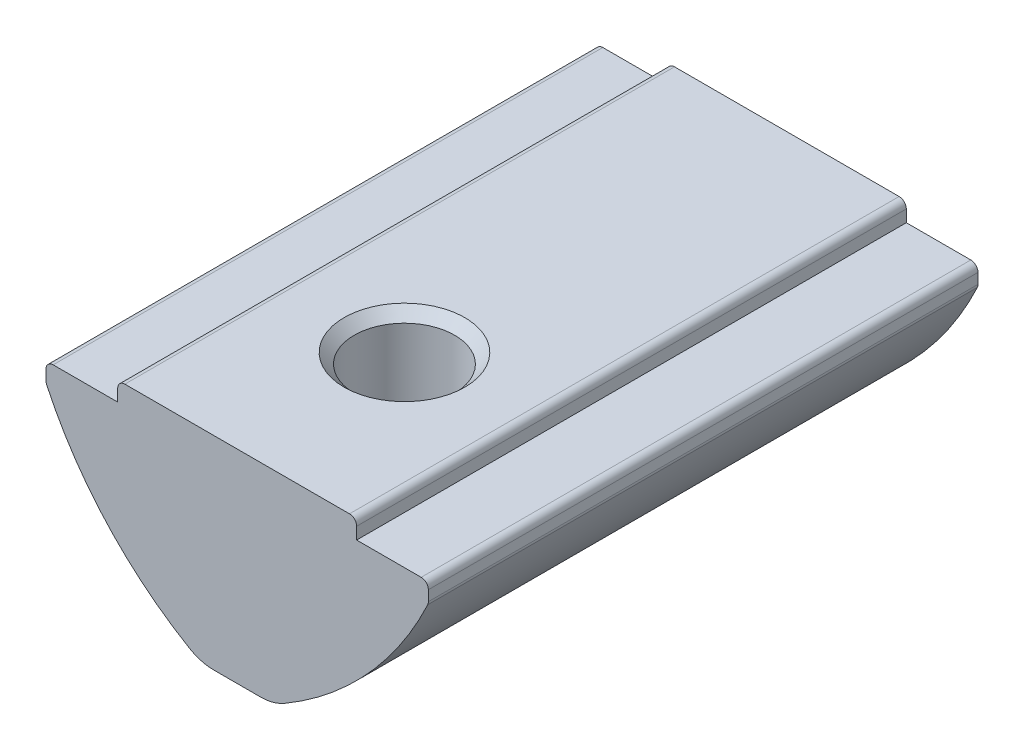
SolidWorks part; units mm, degrees
ref_plane "Спереди" through (0, 0, 0) normal (0, 0, 1) x (1, 0, 0)
ref_plane "Сверху" through (0, 0, 0) normal (0, 1, 0) x (1, 0, 0)
ref_plane "Справа" through (0, 0, 0) normal (1, 0, 0) x (0, 0, -1)
sketch "Эскиз1" plane through (0, 0, 0) normal (0, 0, 1) x (1, 0, 0)
  line L0 (-5, 0) -> (5, 0)
  line L5 (-5, 0) -> (-5, -0.8)
  line L6 (-5, -0.8) -> (-8, -0.8)
  line L7 (-8, -0.8) -> (-8, -1.6)
  line L8 (5, 0) -> (5, -0.8)
  line L9 (5, -0.8) -> (8, -0.8)
  line L10 (8, -0.8) -> (8, -1.6)
  line L11 (-1.5, -8.5) -> (1.5, -8.5)
  arc A0 (-8, -1.6) -> (-1.5, -8.5) centre (5.609, 4.7084) ccw
  arc A1 (1.5, -8.5) -> (8, -1.6) centre (-5.609, 4.7084) ccw
  point P0 (0, -8.5)
  point P4 (0, 0)
  dimension "D7" = 15
  dimension "D1" = 10
  dimension "D2" = 16
  dimension "D3" = 0.8
  dimension "D4" = 3
  dimension "D5" = 0.8
  dimension "D6" = 8.5
extrude "Бобышка-Вытянуть1" add sketch "Эскиз1" along normal mid plane 23
fillet "Скругление1" radius 0.3 6 edges at (8, -1.6, 0) (8, -0.8, 0) (-8, -0.8, 0) (-8, -1.6, 0) (5, 0, 0) (-5, 0, 0)
fillet "Скругление2" radius 2 2 edges at (1.5, -8.5, 0) (-1.5, -8.5, 0)
hole_wizard "Отверстие обработанное метчиком M53" positions "Эскиз2" profile "Эскиз4" tap size "M5" standard "ISO" end condition through all
sketch "Эскиз2" plane through (0, 0, 0) normal (0, 1, 0) x (1, 0, 0)
  line L0 (4.7, -11.5) -> (-4.7, -11.5) construction
  point P0 (0, -4.5)
  dimension "D1" = 7
sketch "Эскиз4" plane through (0, 0, 4.5) normal (1, 0, 0) x (0, 0, 1)
  line L0 (0, 0) -> (0, 8.5)
  line L1 (0, 8.5) -> (2.1, 8.5)
  line L2 (2.1, 8.5) -> (2.1, 0.425)
  line L3 (2.1, 0.425) -> (2.525, 0)
  line L5 (2.525, 0) -> (0, 0)
  line L6 (-2.1, 0.425) -> (-2.525, 0) construction
  line L11 (0, -6.35) -> (0, 107.95) construction
  dimension "Диаметр проходного сверла" = 4.2
  dimension "Глубина проходного сверла" = 8.5
  dimension "Диаметр передней зенковки" = 5.05
  dimension "Угол передней зенковки" = 90
cosmetic thread "Отверстие резьбы1" parameters "D2"=5
sketch "Эскиз5" plane through (0, 0, 0) normal (1, 0, 0) x (0, 0, -1)
  line L1 (6.5, -4.3) -> (6.5, -9.3) construction
  line L2 (11.5, -8.2244) -> (11.5, -1.6609) construction
  line L3 (6.5, -4.3) -> (6.5, -9.3)
  line L5 (11.5, -8.5) -> (-2.641, -8.5) construction
  arc A0 (6.5, -4.3) -> (6.5, -9.3) centre (6.5, -6.8) ccw
  point P3 (4, -7.4722)
  dimension "D3" = 2.5
  dimension "D1" = 0.8
  dimension "D2" = 5
revolve "Повернуть1" add sketch "Эскиз5" angle 360 about L1
